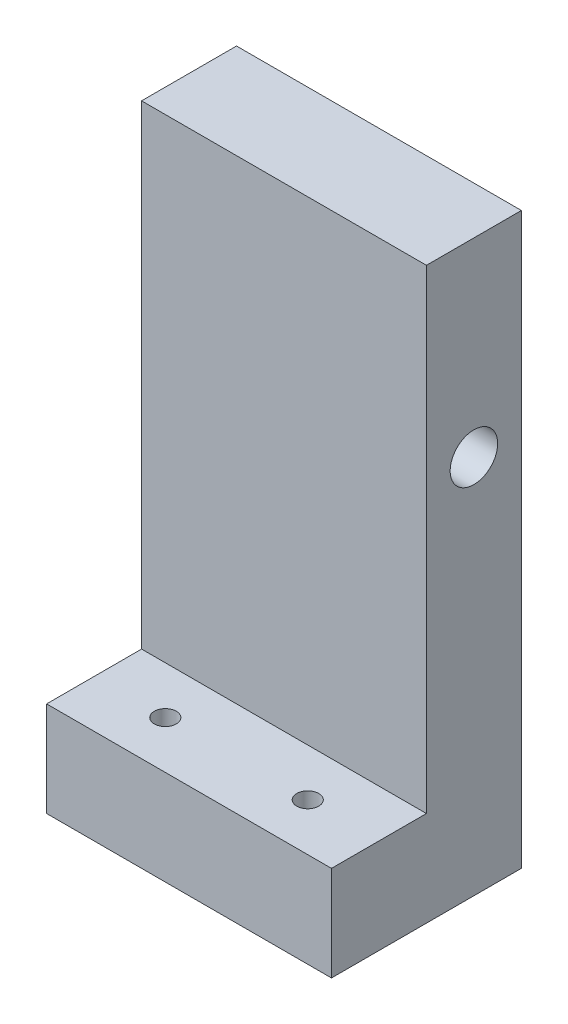
SolidWorks part; units mm, degrees
ref_plane "Front Plane" through (0, 0, 0) normal (0, 0, 1) x (1, 0, 0)
ref_plane "Top Plane" through (0, 0, 0) normal (0, 1, 0) x (1, 0, 0)
ref_plane "Right Plane" through (0, 0, 0) normal (1, 0, 0) x (0, 0, -1)
sketch "Sketch1" plane through (0, 0, 0) normal (1, 0, 0) x (0, 0, -1)
  line L0 (0, 0) -> (0, 12.7)
  line L1 (0, 12.7) -> (12.7, 12.7)
  line L4 (25.4, 0) -> (25.4, 76.2)
  line L5 (25.4, 76.2) -> (12.7, 76.2)
  line L6 (12.7, 76.2) -> (12.7, 12.7)
  line L7 (0, 0) -> (25.4, 0)
  dimension "D1" = 76.2
  dimension "D2" = 25.4
  dimension "D3" = 12.7
  dimension "D4" = 12.7
extrude "Boss-Extrude1" add sketch "Sketch1" along normal blind 38.1
sketch "Sketch2" plane through (38.1, 0, 0) normal (1, 0, 0) x (0, 0, -1)
  line L0 (19.05, 76.2) -> (19.05, 0) construction
  line L1 (25.4, 76.2) -> (12.7, 76.2) construction
  line L2 (0, 0) -> (25.4, 0) construction
  circle A0 centre (19.05, 50.8) radius 3.175
  dimension "D2" = 6.35
  dimension "D1" = 50.8
extrude "Cut-Extrude1" cut sketch "Sketch2" against normal through all
sketch "Sketch3" plane through (0, 12.7, 0) normal (0, 1, 0) x (1, 0, 0)
  line L0 (0, 6.35) -> (38.1, 6.35) construction
  line L1 (0, 12.7) -> (0, 0) construction
  line L2 (38.1, 12.7) -> (38.1, 0) construction
  circle A0 centre (9.525, 6.35) radius 1.4732
  circle A1 centre (28.575, 6.35) radius 1.4732
  dimension "D3" = 2.9464
  dimension "D1" = 19.05
  dimension "D2" = 9.525
extrude "Cut-Extrude2" cut sketch "Sketch3" against normal through all
